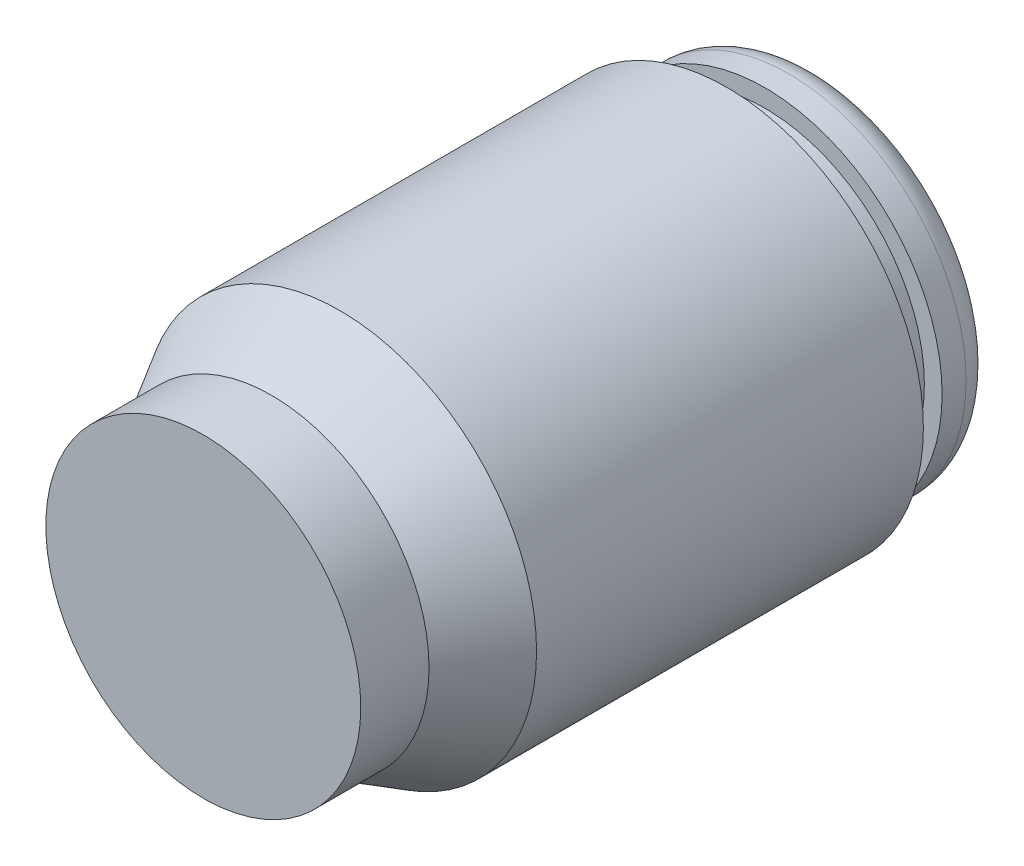
SolidWorks part; units mm, degrees
ref_plane "Front Plane" through (0, 0, 0) normal (0, 0, 1) x (1, 0, 0)
ref_plane "Top Plane" through (0, 0, 0) normal (0, 1, 0) x (1, 0, 0)
ref_plane "Right Plane" through (0, 0, 0) normal (1, 0, 0) x (0, 0, -1)
sketch "Sketch1" plane through (0, 0, 0) normal (1, 0, 0) x (0, 0, -1)
  line L0 (14.859, 4.6863) -> (15.494, 4.6863)
  line L1 (3.61, 5.207) -> (13.843, 5.207)
  line L2 (0, 4.1656) -> (0, 0)
  line L3 (3.61, 3.175) -> (15.875, 3.175)
  line L4 (16.256, 3.9243) -> (16.256, 3.556)
  line L5 (3.61, 3.175) -> (3.61, 0)
  line L6 (13.843, 5.207) -> (13.843, 4.2177)
  line L7 (13.843, 4.2177) -> (14.859, 4.2177)
  line L8 (14.859, 4.6863) -> (14.859, 4.2177)
  line L9 (3.61, 0) -> (0, 0)
  line L10 (0, 0) -> (16.256, 0) construction
  line L12 (15.875, 3.175) -> (16.256, 3.556)
  line L14 (0, 4.1656) -> (1.8062, 4.1656)
  line L15 (1.8062, 4.1656) -> (3.61, 5.207)
  arc A0 (15.494, 4.6863) -> (16.256, 3.9243) centre (15.494, 3.9243) cw
  point P1 (16.256, 3.175)
  point P20 (16.256, 4.6863)
  dimension "D4" = 0.762
  dimension "tube od" = 6.35
  dimension "D1" = 1.397
  dimension "D2" = 1.016
  dimension "D3" = 8.4353
  dimension "D6" = 9.3726
  dimension "D9" = 30
  dimension "D10" = 8.3312
  dimension "D5" = 14.4498
revolve "Revolve1" add sketch "Sketch1" angle 360 about L10
equation "\"D6@Sketch1\" = \"G@Sketch1\"*.9"
equation "\"D3@Sketch1\" = \"D6@Sketch1\"*.9"
equation "\"D10@Sketch1\" = \"G@Sketch1\"*.8"
equation "\"D5@Sketch1\" = \"H@Sketch1\"/1.125"
